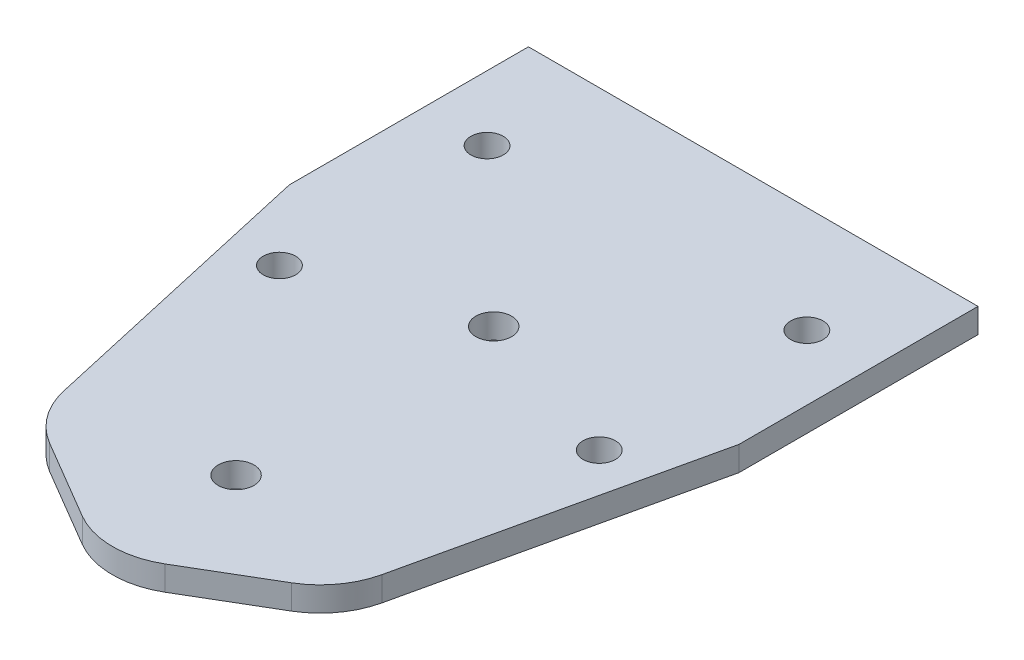
SolidWorks part; units mm, degrees
material "PC High Viscosity"
ref_plane "Front Plane" through (0, 0, 0) normal (0, 0, 1) x (1, 0, 0)
ref_plane "Top Plane" through (0, 0, 0) normal (0, 1, 0) x (1, 0, 0)
ref_plane "Right Plane" through (0, 0, 0) normal (1, 0, 0) x (0, 0, -1)
sketch "Sketch1" plane through (0, 0, 0) normal (0, 1, 0) x (1, 0, 0)
  line L1 (-27.5, -40) -> (27.5, -40)
  line L2 (-27.5, -40) -> (-27.5, 40)
  line L3 (-27.5, 40) -> (27.5, 40)
  line L4 (27.5, -40) -> (27.5, 40)
  line L5 (-27.5, -40) -> (27.5, 40) construction
  line L6 (-27.5, 40) -> (27.5, -40) construction
  point P0 (0, 0)
  dimension "D1" = 55
  dimension "D2" = 80
extrude "Boss-Extrude1" add sketch "Sketch1" along normal blind 3
sketch "Sketch2" plane through (0, 3, 0) normal (0, 1, 0) x (1, 0, 0)
  line L0 (0, 40) -> (0, -40) construction
  line L1 (27.5, 40) -> (-27.5, 40) construction
  line L2 (-27.5, -40) -> (27.5, -40) construction
  line L3 (27.5, 40) -> (-27.5, 40) construction
  line L4 (-27.5, 40) -> (-27.5, -40) construction
  circle A0 centre (0, 8.25) radius 2.185
  circle A1 centre (0, -23.271) radius 2.185
  circle A2 centre (-19.5625, 27) radius 1.9844
  circle A3 centre (-19.5625, 1.6) radius 1.9844
  circle A4 centre (19.5625, 27) radius 1.9844
  circle A5 centre (19.5625, 1.6) radius 1.9844
  dimension "D1" = 4.37
  dimension "D2" = 31.521
  dimension "D3" = 31.75
  dimension "D4" = 25.4
  dimension "D5" = 3.9688
  dimension "D6" = 7.9375
  dimension "D7" = 13
extrude "Cut-Extrude1" cut sketch "Sketch2" against normal through all
sketch "Sketch3" plane through (0, 3, 0) normal (0, 1, 0) x (1, 0, 0)
  line L0 (0, -40) -> (27.5, -40)
  line L1 (-27.5, -40) -> (27.5, -40) construction
  line L5 (27.5, -40) -> (27.5, 10.7529)
  line L6 (27.5, -40) -> (27.5, 40) construction
  line L7 (27.5, 10.7529) -> (18.5103, -29.0945)
  line L8 (18.5103, -29.0945) -> (0, -40)
  line M7 (27.5, -40) -> (27.5, 40)
  line M12 (-27.5, -40) -> (27.5, -40)
extrude "Cut-Extrude2" cut sketch "Sketch3" against normal through all contours L7 L8 M12 M7
mirror "Mirror1" about plane through (0, 0, 0) normal (1, 0, 0) of "Cut-Extrude2"
fillet "Fillet1" radius 10 3 edges at (18.5103, 1.5, 29.0945) (0, 1.5, 40) (-18.5103, 1.5, 29.0945)
equation "\"pulley_pitch_diam\"= 12.73mm"
equation "\"pulley_total_width\"= 16mm"
equation "\"pulley_total_diam\"= 16mm"
equation "\"belt_width\"= 6mm"
equation "\"material_thickness\"= 3mm"
equation "\"shaft_diam\"= 8mm"
equation "\"bearing_od\"= 22mm"
equation "\"bearing_thickness\"= 7mm"
equation "\"D1@Boss-Extrude1\"=\"material_thickness\""
